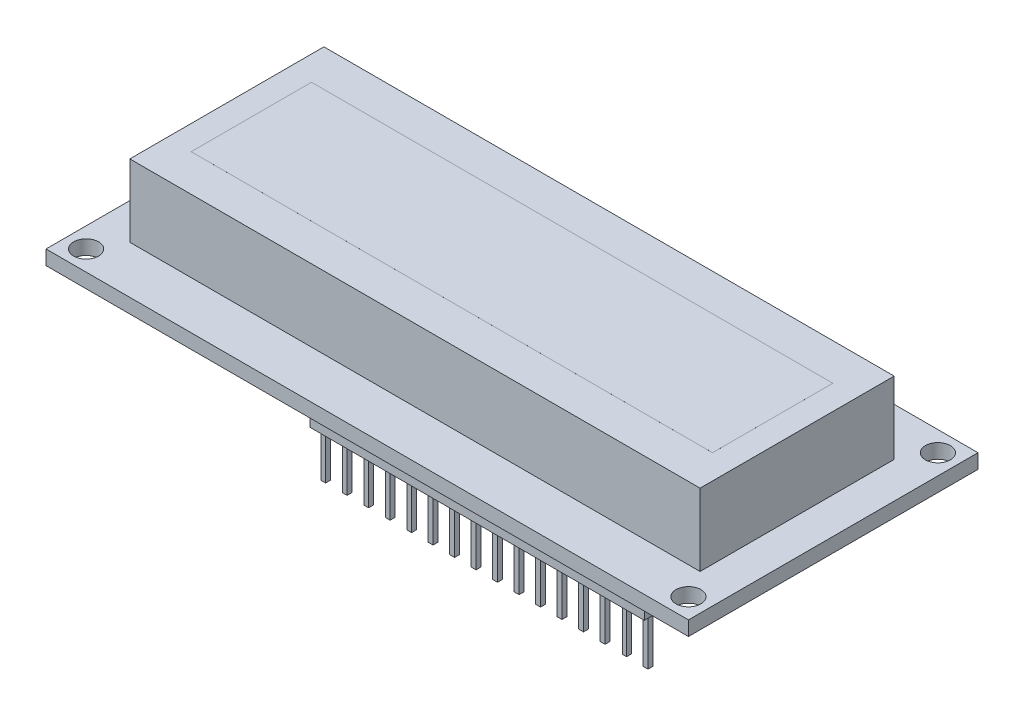
SolidWorks part; units mm, degrees
ref_plane "Front Plane" through (0, 0, 0) normal (0, 0, 1) x (1, 0, 0)
ref_plane "Top Plane" through (0, 0, 0) normal (0, 1, 0) x (1, 0, 0)
ref_plane "Right Plane" through (0, 0, 0) normal (1, 0, 0) x (0, 0, -1)
sketch "Sketch1" plane through (0, 0, 0) normal (0, 1, 0) x (1, 0, 0)
  line L1 (35.55, -12.1) -> (-35.55, -12.1)
  line L2 (35.55, -12.1) -> (35.55, 12.1)
  line L3 (35.55, 12.1) -> (-35.55, 12.1)
  line L4 (-35.55, -12.1) -> (-35.55, 12.1)
  line L5 (35.55, -12.1) -> (-35.55, 12.1) construction
  line L6 (35.55, 12.1) -> (-35.55, -12.1) construction
  point P0 (0, 0)
  dimension "D1" = 71.1
  dimension "D2" = 24.2
extrude "Boss-Extrude1" add sketch "Sketch1" along normal blind 6
sketch "Sketch2" plane through (0, 0, 0) normal (0, -1, 0) x (1, 0, 0)
  line L1 (-35.55, 9.1) -> (-38.05, 9.1)
  line L2 (-35.55, 9.1) -> (-35.55, -9.1)
  line L3 (-35.55, -9.1) -> (-38.05, -9.1)
  line L4 (-35.55, 12.1) -> (-35.55, -12.1)
  line L5 (-35.55, -12.1) -> (35.55, -12.1)
  line L6 (35.55, -12.1) -> (35.55, 12.1)
  line L7 (35.55, 12.1) -> (-35.55, 12.1)
  line L8 (-35.55, 12.1) -> (-35.55, -12.1)
  line L9 (-35.55, -12.1) -> (35.55, -12.1)
  line L10 (35.55, -12.1) -> (35.55, 12.1)
  line L11 (35.55, 12.1) -> (-35.55, 12.1)
  line L12 (-38.05, 9.1) -> (-38.05, -9.1)
  line M5 (-35.55, 12.1) -> (-35.55, -12.1)
  line M6 (-35.55, -12.1) -> (35.55, -12.1)
  line M7 (35.55, -12.1) -> (35.55, 12.1)
  line M8 (35.55, 12.1) -> (-35.55, 12.1)
  dimension "D2" = 18.2
  dimension "D3" = 9.1
  dimension "D4" = 2.5
  dimension "D1" = 0
extrude "Boss-Extrude2" add sketch "Sketch2" along normal blind 3 contours M8 M5 M6 M7 | L1 L12 L3 M5
sketch "Sketch3" plane through (0, -3, 0) normal (0, -1, 0) x (1, 0, 0)
  line L0 (0, 0) -> (0, -5.5613) construction
  line L1 (40.05, -18.05) -> (-40.05, -18.05)
  line L2 (40.05, -18.05) -> (40.05, 18.05)
  line L3 (40.05, 18.05) -> (-40.05, 18.05)
  line L4 (-40.05, -18.05) -> (-40.05, 18.05)
  line L5 (40.05, -18.05) -> (-40.05, 18.05) construction
  line L6 (40.05, 18.05) -> (-40.05, -18.05) construction
  line L7 (0, 0) -> (6.3147, 0) construction
  circle A0 centre (-37.55, -15.55) radius 1.55
  circle A1 centre (37.55, -15.55) radius 1.55
  circle A2 centre (37.55, 15.55) radius 1.55
  circle A3 centre (-37.55, 15.55) radius 1.55
  point P0 (0, 0)
  dimension "D3" = 3.1
  dimension "D1" = 36.1
  dimension "D2" = 80.1
  dimension "D4" = 2.5
  dimension "D5" = 2.5
extrude "Boss-Extrude3" add sketch "Sketch3" along normal blind 1.8
sketch "Sketch4" plane through (0, 6, 0) normal (0, 1, 0) x (1, 0, 0)
  line L1 (32.5, -7.5) -> (-32.5, -7.5)
  line L2 (32.5, -7.5) -> (32.5, 7.5)
  line L3 (32.5, 7.5) -> (-32.5, 7.5)
  line L4 (-32.5, -7.5) -> (-32.5, 7.5)
  line L5 (32.5, -7.5) -> (-32.5, 7.5) construction
  line L6 (32.5, 7.5) -> (-32.5, -7.5) construction
  point P0 (0, 0)
  dimension "D1" = 65
  dimension "D2" = 15
extrude "Boss-Extrude4" add sketch "Sketch4" along normal blind 0.001 and the other way blind 6
sketch "Sketch5" plane through (0, -4.8, 0) normal (0, -1, 0) x (1, 0, 0)
  line L0 (40.05, 18.05) -> (-40.05, 18.05) construction
  line L1 (-8.65, 16.55) -> (33.05, 16.55)
  line L2 (-8.65, 16.55) -> (-8.65, 14.05)
  line L3 (-8.65, 14.05) -> (33.05, 14.05)
  line L4 (33.05, 16.55) -> (33.05, 14.05)
  line L5 (40.05, -18.05) -> (40.05, 18.05) construction
  dimension "D1" = 41.7
  dimension "D2" = 2.5
  dimension "D3" = 1.5
  dimension "D4" = 7
extrude "Boss-Extrude5" add sketch "Sketch5" along normal blind 2.5
sketch "Sketch6" plane through (0, -7.3, 0) normal (0, -1, 0) x (1, 0, 0)
  line L0 (33.05, 14.05) -> (33.05, 16.55) construction
  line L1 (31.95, 14.9922) -> (32.55, 14.9922)
  line L2 (31.95, 14.9922) -> (31.95, 15.5922)
  line L3 (31.95, 15.5922) -> (32.55, 15.5922)
  line L4 (32.55, 14.9922) -> (32.55, 15.5922)
  line L5 (31.95, 14.9922) -> (32.55, 15.5922) construction
  line L6 (31.95, 15.5922) -> (32.55, 14.9922) construction
  line L7 (29.35, 15.5922) -> (29.95, 15.5922)
  line L8 (29.35, 14.9922) -> (29.35, 15.5922)
  line L9 (29.35, 14.9922) -> (29.95, 14.9922)
  line L10 (29.95, 14.9922) -> (29.95, 15.5922)
  line L11 (29.27, 14.9922) -> (29.27, 15.5922)
  line L12 (29.27, 15.5922) -> (29.87, 15.5922)
  line L13 (29.27, 14.9922) -> (29.87, 14.9922)
  line L14 (29.87, 14.9922) -> (29.87, 15.5922)
  line L15 (26.59, 14.9922) -> (26.59, 15.5922)
  line L16 (26.59, 15.5922) -> (27.19, 15.5922)
  line L17 (26.59, 14.9922) -> (27.19, 14.9922)
  line L18 (27.19, 14.9922) -> (27.19, 15.5922)
  line L19 (23.91, 14.9922) -> (23.91, 15.5922)
  line L20 (23.91, 15.5922) -> (24.51, 15.5922)
  line L21 (23.91, 14.9922) -> (24.51, 14.9922)
  line L22 (24.51, 14.9922) -> (24.51, 15.5922)
  line L23 (21.23, 14.9922) -> (21.23, 15.5922)
  line L24 (21.23, 15.5922) -> (21.83, 15.5922)
  line L25 (21.23, 14.9922) -> (21.83, 14.9922)
  line L26 (21.83, 14.9922) -> (21.83, 15.5922)
  line L27 (18.55, 14.9922) -> (18.55, 15.5922)
  line L28 (18.55, 15.5922) -> (19.15, 15.5922)
  line L29 (18.55, 14.9922) -> (19.15, 14.9922)
  line L30 (19.15, 14.9922) -> (19.15, 15.5922)
  line L31 (15.87, 14.9922) -> (15.87, 15.5922)
  line L32 (15.87, 15.5922) -> (16.47, 15.5922)
  line L33 (15.87, 14.9922) -> (16.47, 14.9922)
  line L34 (16.47, 14.9922) -> (16.47, 15.5922)
  line L35 (13.19, 14.9922) -> (13.19, 15.5922)
  line L36 (13.19, 15.5922) -> (13.79, 15.5922)
  line L37 (13.19, 14.9922) -> (13.79, 14.9922)
  line L38 (13.79, 14.9922) -> (13.79, 15.5922)
  line L39 (10.51, 14.9922) -> (10.51, 15.5922)
  line L40 (10.51, 15.5922) -> (11.11, 15.5922)
  line L41 (10.51, 14.9922) -> (11.11, 14.9922)
  line L42 (11.11, 14.9922) -> (11.11, 15.5922)
  line L43 (7.83, 14.9922) -> (7.83, 15.5922)
  line L44 (7.83, 15.5922) -> (8.43, 15.5922)
  line L45 (7.83, 14.9922) -> (8.43, 14.9922)
  line L46 (8.43, 14.9922) -> (8.43, 15.5922)
  line L47 (5.15, 14.9922) -> (5.15, 15.5922)
  line L48 (5.15, 15.5922) -> (5.75, 15.5922)
  line L49 (5.15, 14.9922) -> (5.75, 14.9922)
  line L50 (5.75, 14.9922) -> (5.75, 15.5922)
  line L51 (2.47, 14.9922) -> (2.47, 15.5922)
  line L52 (2.47, 15.5922) -> (3.07, 15.5922)
  line L53 (2.47, 14.9922) -> (3.07, 14.9922)
  line L54 (3.07, 14.9922) -> (3.07, 15.5922)
  line L55 (-0.21, 14.9922) -> (-0.21, 15.5922)
  line L56 (-0.21, 15.5922) -> (0.39, 15.5922)
  line L57 (-0.21, 14.9922) -> (0.39, 14.9922)
  line L58 (0.39, 14.9922) -> (0.39, 15.5922)
  line L59 (-2.89, 14.9922) -> (-2.89, 15.5922)
  line L60 (-2.89, 15.5922) -> (-2.29, 15.5922)
  line L61 (-2.89, 14.9922) -> (-2.29, 14.9922)
  line L62 (-2.29, 14.9922) -> (-2.29, 15.5922)
  line L63 (-5.57, 14.9922) -> (-5.57, 15.5922)
  line L64 (-5.57, 15.5922) -> (-4.97, 15.5922)
  line L65 (-5.57, 14.9922) -> (-4.97, 14.9922)
  line L66 (-4.97, 14.9922) -> (-4.97, 15.5922)
  line L67 (-8.25, 14.9922) -> (-8.25, 15.5922)
  line L68 (-8.25, 15.5922) -> (-7.65, 15.5922)
  line L69 (-8.25, 14.9922) -> (-7.65, 14.9922)
  line L70 (-7.65, 14.9922) -> (-7.65, 15.5922)
  point P0 (32.25, 15.2922)
  dimension "D1" = 0.6
  dimension "D2" = 0.5
  dimension "D4" = 2
  dimension "D6" = 0.6
  dimension "D3" = 2
  dimension "D5" = 16
extrude "Boss-Extrude6" add sketch "Sketch6" along normal blind 6 contours L1 L4 L3 L2 | L9 L14 L7 L8 | L17 L18 L16 L15 | L21 L22 L20 L19 | L25 L26 L24 L23 | L29 L30 L28 L27 | L33 L34 L32 L31 | L37 L38 L36 L35 | L41 L42 L40 L39 | L45 L46 L44 L43 | L49 L50 L48 L47 | L53 L54 L52 L51 | L69 L70 L68 L67 | L65 L66 L64 L63 | L57 L58 L56 L55 | L59 L60 L62 L61
